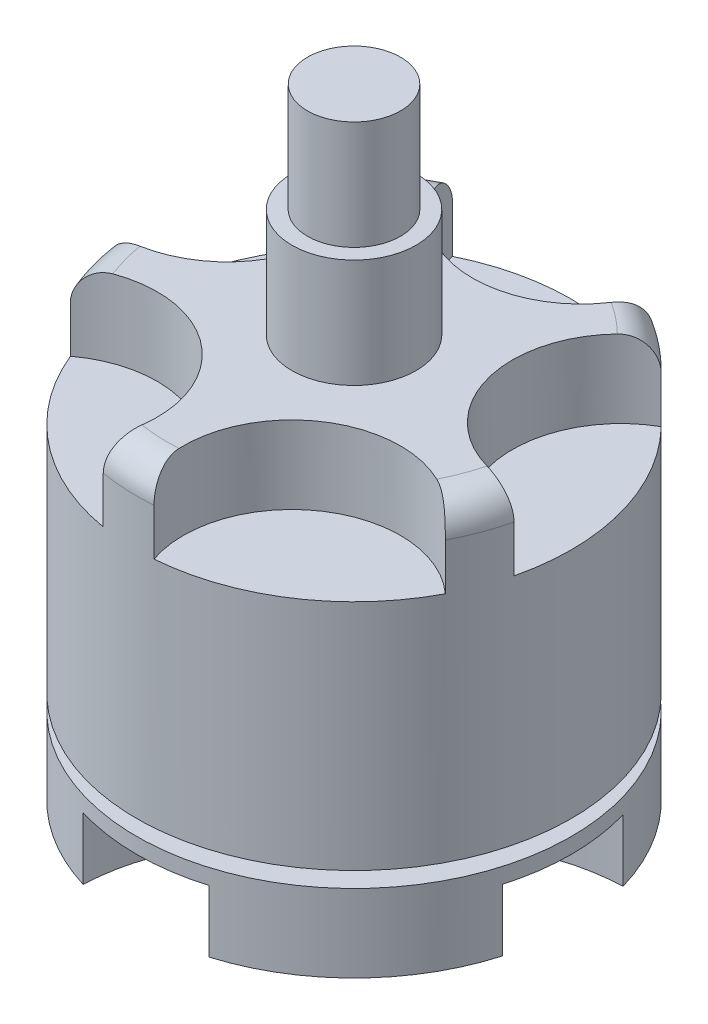
SolidWorks part; units mm, degrees
ref_plane "Front Plane" through (0, 0, 0) normal (0, 0, 1) x (1, 0, 0)
ref_plane "Top Plane" through (0, 0, 0) normal (0, 1, 0) x (1, 0, 0)
ref_plane "Right Plane" through (0, 0, 0) normal (1, 0, 0) x (0, 0, -1)
sketch "Sketch1" plane through (0, 0, 0) normal (0, 1, 0) x (1, 0, 0)
  circle A0 centre (0, 0) radius 14
  dimension "D1" = 28
extrude "Boss-Extrude1" add sketch "Sketch1" along normal blind 26
sketch "Sketch2" plane through (0, 26, 0) normal (0, 1, 0) x (1, 0, 0)
  circle A0 centre (0, 0) radius 4
  dimension "D1" = 8
extrude "Boss-Extrude2" add sketch "Sketch2" along normal blind 7
sketch "Sketch3" plane through (0, 33, 0) normal (0, 1, 0) x (1, 0, 0)
  circle A0 centre (0, 0) radius 3
  dimension "D1" = 6
extrude "Boss-Extrude3" add sketch "Sketch3" along normal blind 7
cosmetic thread "Cosmetic Thread1" parameters "D2"=4.891
sketch "Sketch5" plane through (0, 0, 0) normal (0, -1, 0) x (1, 0, 0)
  circle A0 centre (0, 0) radius 5
  dimension "D1" = 10
extrude "Cut-Extrude1" cut sketch "Sketch5" against normal blind 5
sketch "Sketch7" plane through (0, 26, 0) normal (0, 1, 0) x (1, 0, 0)
  circle A0 centre (-13.0996, 4.9396) radius 7
  circle A1 centre (0, 0) radius 14 construction
  circle A2 centre (-8.7459, -10.9321) radius 7
  circle A3 centre (7.6944, -11.696) radius 7
  circle A4 centre (13.5012, 3.7036) radius 7
  circle A5 centre (0.6498, 13.9849) radius 7
  point P14 (-13.0093, 5.1728)
  dimension "D1" = 14
  dimension "D2" = 14
  dimension "D3" = 14
  dimension "D4" = 14
  dimension "D5" = 14
  dimension "D6" = 16.458
  dimension "D7" = 16.458
  dimension "D8" = 16.458
  dimension "D9" = 16.458
extrude "Cut-Extrude2" cut sketch "Sketch7" against normal blind 5
fillet "Fillet1" radius 2 5 edges at (-7.6944, 26, -11.696) (8.7458, 26, -10.9321) (13.0996, 26, 4.9396) (-0.6498, 26, 13.9849) (-13.5013, 26, 3.7035)
sketch "Sketch9" plane through (0, 0, 0) normal (0, -1, 0) x (1, 0, 0)
  circle A0 centre (0, 0) radius 14 construction
  circle A1 centre (0, 0) radius 5 construction
  arc A3 (-12.4939, 6.3168) -> (-12.4939, -6.3168) centre (0, 0) ccw
  ellipse E0 centre (0, -14) end of major axis (0, -21.5) minor radius 4.0684
  ellipse E1 centre (14, 0) end of major axis (21.5, 0) minor radius 3.8994
  ellipse E2 centre (0, 14) end of major axis (0, 21.5) minor radius 4.0684
  parabola Q0 (-12.4939, -6.3168) -> (-12.4939, 6.3168) focus (-14, 0) apex (-10, 0)
  circle M2 centre (0, 0) radius 14
  dimension "D4" = 10
  dimension "D1" = 6.5
  dimension "D2" = 6.5
  dimension "D3" = 6.5
extrude "Cut-Extrude3" cut sketch "Sketch9" against normal blind 4 contours E2 M2 | E1 M2 | E0 M2 | Q0 M2
ref_plane "Plane1" through (0, 5, 0) normal (0, -1, 0) x (-1, 0, 0)
sketch "Sketch11" plane through (0, 5, 0) normal (0, -1, 0) x (-1, 0, 0)
  circle A0 centre (0, 0) radius 8
  circle A1 centre (0, 0) radius 14
  dimension "D1" = 16
  dimension "D2" = 28
extrude "Cut-Extrude4" cut sketch "Sketch11" against normal blind 1
